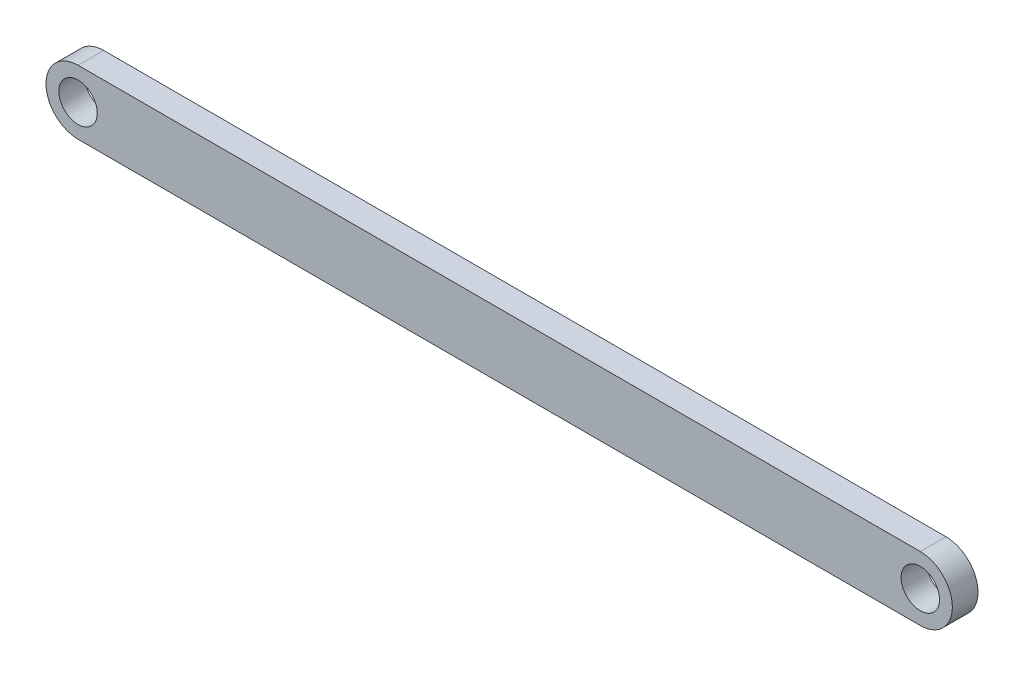
SolidWorks part; units mm, degrees
ref_plane "Front Plane" through (0, 0, 0) normal (0, 0, 1) x (1, 0, 0)
ref_plane "Top Plane" through (0, 0, 0) normal (0, 1, 0) x (1, 0, 0)
ref_plane "Right Plane" through (0, 0, 0) normal (1, 0, 0) x (0, 0, -1)
sketch "Sketch1" plane through (0, 0, 0) normal (0, 0, 1) x (1, 0, 0)
  line L0 (0.0945, -0.0083) -> (65.7945, -0.0083) construction
  line L1 (0.0945, 2.4917) -> (65.7945, 2.4917)
  line L2 (0.0945, -2.5083) -> (65.7945, -2.5083)
  arc A0 (0.0945, 2.4917) -> (0.0945, -2.5083) centre (0.0945, -0.0083) ccw
  arc A1 (65.7945, -2.5083) -> (65.7945, 2.4917) centre (65.7945, -0.0083) ccw
  circle A2 centre (0.0945, -0.0083) radius 1.5
  circle A3 centre (65.7945, -0.0083) radius 1.5
  point P2 (32.9445, -0.0083)
  dimension "D3" = 3
  dimension "D4" = 3
  dimension "D1" = 65.7
  dimension "D2" = 5
extrude "Boss-Extrude1" add sketch "Sketch1" along normal blind 2
